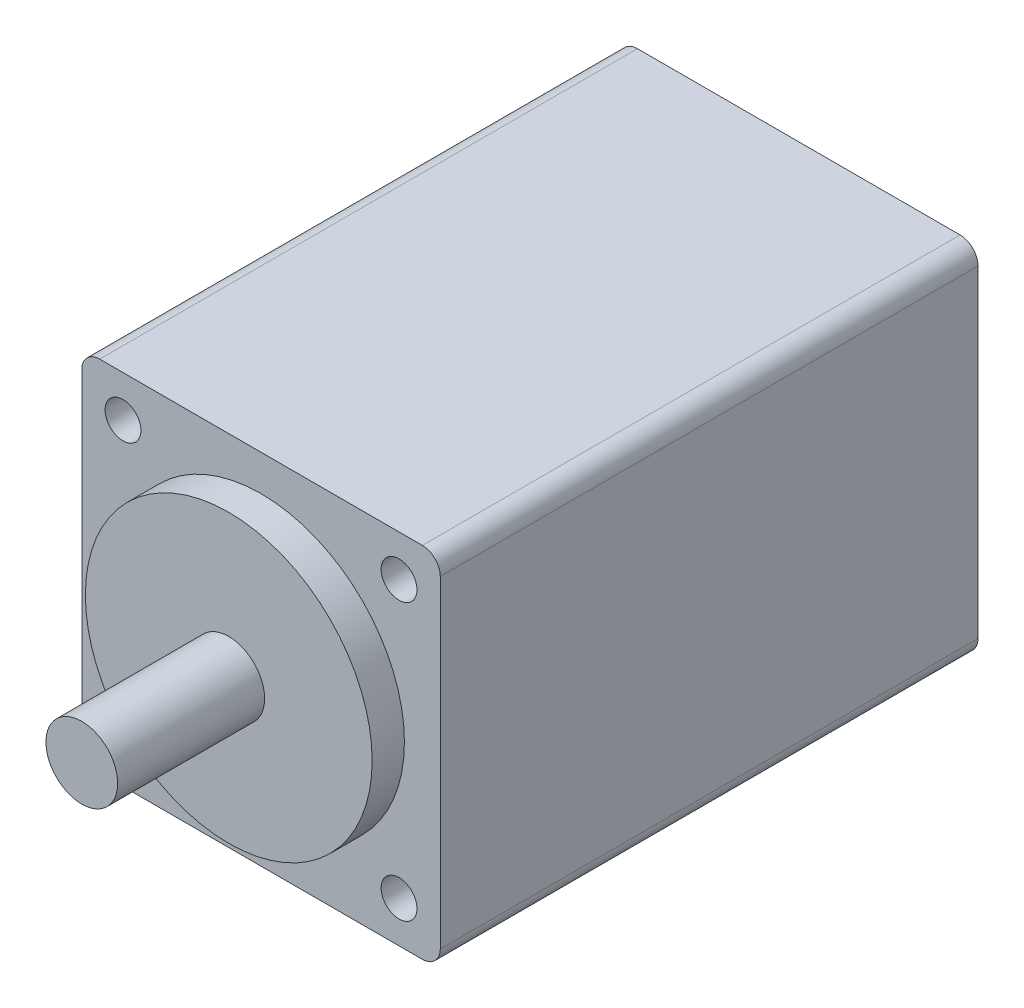
SolidWorks part; units mm, degrees
ref_plane "Front Plane" through (0, 0, 0) normal (0, 0, 1) x (1, 0, 0)
ref_plane "Top Plane" through (0, 0, 0) normal (0, 1, 0) x (1, 0, 0)
ref_plane "Right Plane" through (0, 0, 0) normal (1, 0, 0) x (0, 0, -1)
sketch "Sketch1" plane through (0, 0, 0) normal (0, 0, 1) x (1, 0, 0)
  line L1 (-10, 10) -> (10, 10)
  line L2 (-10, 10) -> (-10, -10)
  line L3 (-10, -10) -> (10, -10)
  line L4 (10, 10) -> (10, -10)
  line L5 (-10, 10) -> (10, -10) construction
  line L6 (-10, -10) -> (10, 10) construction
  point P0 (0, 0)
  dimension "D1" = 20
  dimension "D2" = 20
extrude "Boss-Extrude1" add sketch "Sketch1" along normal blind 30
fillet "Fillet1" radius 1 4 edges at (-10, -10, 15) (-10, 10, 15) (10, -10, 15) (10, 10, 15)
sketch "Sketch2" plane through (0, 0, 30) normal (0, 0, 1) x (1, 0, 0)
  circle A0 centre (0, 0) radius 8
  dimension "D1" = 16
extrude "Boss-Extrude2" add sketch "Sketch2" along normal blind 1.8
sketch "Sketch3" plane through (0, 0, 31.8) normal (0, 0, 1) x (1, 0, 0)
  circle A0 centre (0, 0) radius 2
  dimension "D1" = 4
extrude "Boss-Extrude3" add sketch "Sketch3" along normal blind 8.2
sketch "Sketch4" plane through (0, 0, 30) normal (0, 0, 1) x (1, 0, 0)
  line L0 (-7.7, 7.7) -> (7.7, -7.7) construction
  circle A0 centre (-7.7, 7.7) radius 1
  circle A1 centre (7.7, 7.7) radius 1
  circle A2 centre (7.7, -7.7) radius 1
  circle A3 centre (-7.7, -7.7) radius 1
  point P8 (0, 0)
  dimension "D1" = 2
  dimension "D2" = 2
  dimension "D3" = 2
  dimension "D4" = 2
  dimension "D5" = 15.4
  dimension "D6" = 15.4
extrude "Cut-Extrude1" cut sketch "Sketch4" against normal blind 3
